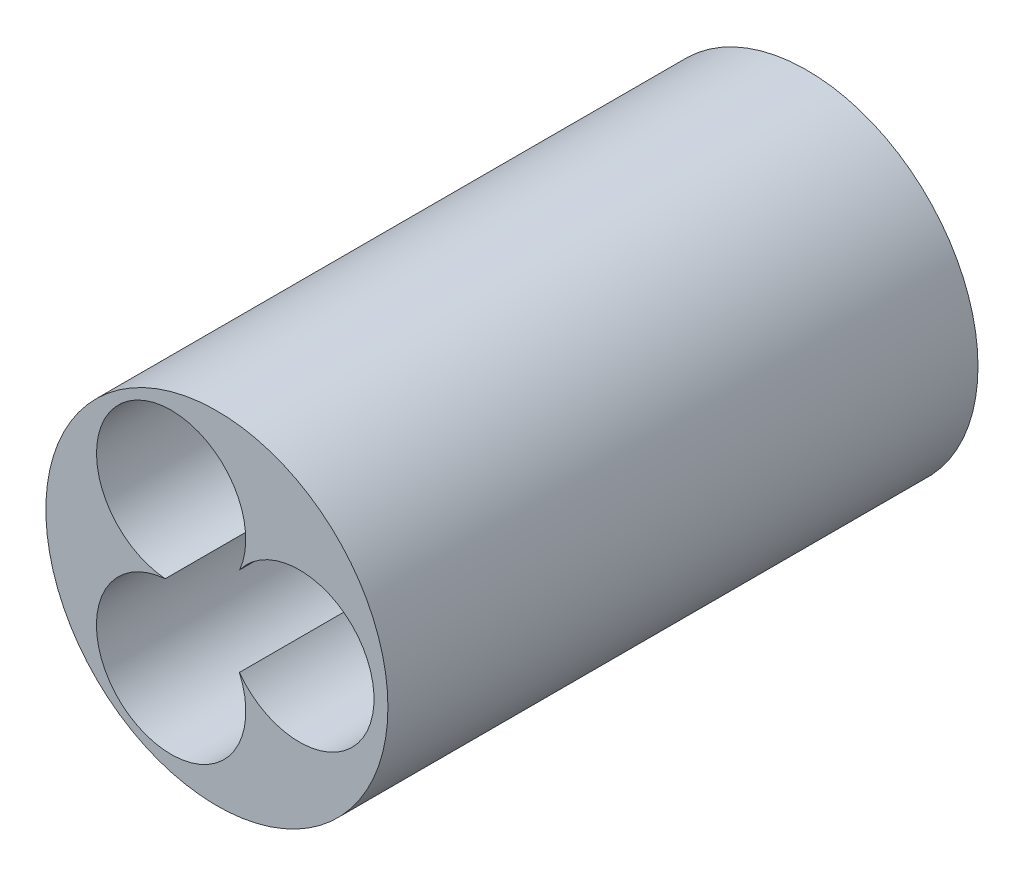
SolidWorks part; units mm, degrees
ref_plane "Front Plane" through (0, 0, 0) normal (0, 0, 1) x (1, 0, 0)
ref_plane "Top Plane" through (0, 0, 0) normal (0, 1, 0) x (1, 0, 0)
ref_plane "Right Plane" through (0, 0, 0) normal (1, 0, 0) x (0, 0, -1)
sketch "Sketch1" plane through (0, 0, 0) normal (0, 0, 1) x (1, 0, 0)
  line L0 (0, 17.6835) -> (0, 0) construction
  line L1 (0, 8.875) -> (15.24, 8.875) construction
  circle A0 centre (0, 0) radius 8.875
  circle A1 centre (0, 17.6835) radius 8.8646
  circle A2 centre (15.24, 8.875) radius 8.8646
  circle A3 centre (5.437, 8.875) radius 20.32
  point P7 (0, 8.875)
  dimension "D1" = 17.75
  dimension "D2" = 17.7292
  dimension "D3" = 15.24
extrude "Boss-Extrude2" add sketch "Sketch1" along normal blind 70.1 contours A3 A2 A0 A1
